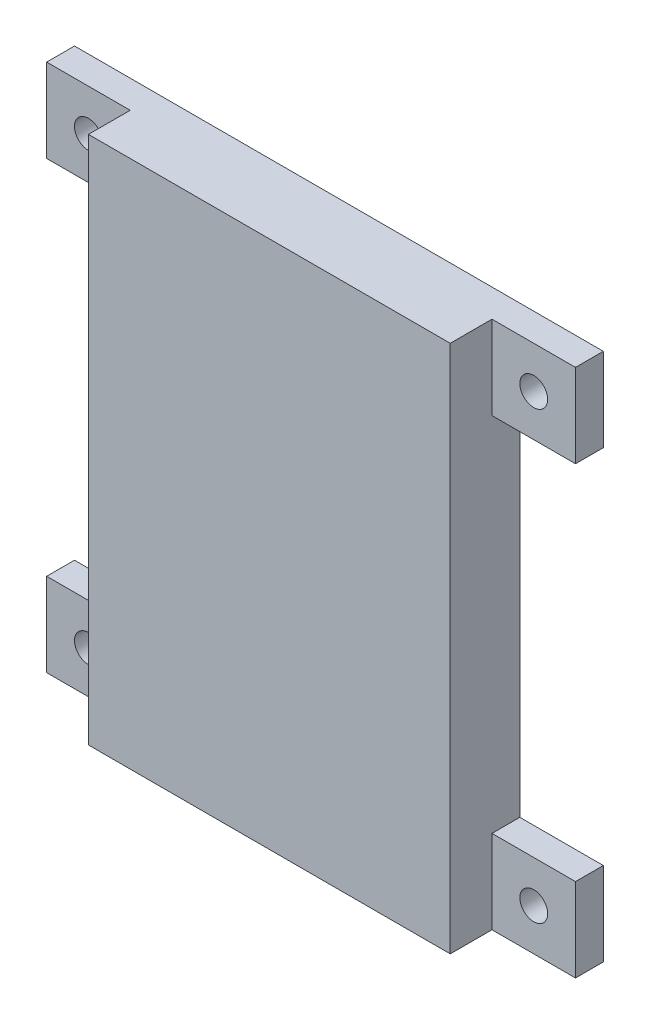
SolidWorks part; units mm, degrees
ref_plane "正面" through (0, 0, 0) normal (0, 0, 1) x (1, 0, 0)
ref_plane "平面" through (0, 0, 0) normal (0, 1, 0) x (1, 0, 0)
ref_plane "右側面" through (0, 0, 0) normal (1, 0, 0) x (0, 0, -1)
sketch "ｽｹｯﾁ1" plane through (0, 0, 0) normal (0, 0, 1) x (1, 0, 0)
  line L1 (13, -19) -> (-13, -19)
  line L2 (13, -19) -> (13, 19)
  line L3 (13, 19) -> (-13, 19)
  line L4 (-13, -19) -> (-13, 19)
  line L5 (13, -19) -> (-13, 19) construction
  line L6 (13, 19) -> (-13, -19) construction
  point P0 (0, 0)
  dimension "D1" = 38
  dimension "D2" = 26
extrude "ﾎﾞｽ - 押し出し1" add sketch "ｽｹｯﾁ1" along normal blind 5
sketch "ｽｹｯﾁ2" plane through (0, 0, 0) normal (0, 0, 1) x (1, 0, 0)
  line L1 (11, -17) -> (-11, -17)
  line L2 (11, -17) -> (11, 17)
  line L3 (11, 17) -> (-11, 17)
  line L4 (-11, -17) -> (-11, 17)
  line L5 (11, -17) -> (-11, 17) construction
  line L6 (11, 17) -> (-11, -17) construction
  point P0 (0, 0)
  dimension "D1" = 22
  dimension "D2" = 34
extrude "ｶｯﾄ - 押し出し1" cut sketch "ｽｹｯﾁ2" along normal blind 3
sketch "ｽｹｯﾁ3" plane through (0, 0, 0) normal (0, 0, 1) x (1, 0, 0)
  line L0 (13, 19) -> (-13, 19) construction
  line L1 (-0.8522, 2) -> (1.1478, 2)
  line L2 (-0.8522, 2) -> (-0.8522, 9)
  line L3 (-0.8522, 9) -> (1.1478, 9)
  line L4 (1.1478, 2) -> (1.1478, 9)
  line L5 (-0.8522, 2) -> (1.1478, 9) construction
  line L6 (-0.8522, 9) -> (1.1478, 2) construction
  point P0 (0.1478, 5.5)
  dimension "D1" = 7
  dimension "D2" = 2
  dimension "D3" = 10
sketch "ｽｹｯﾁ4" plane through (0, 0, 0) normal (0, 0, 1) x (1, 0, 0)
  line L0 (13, -19) -> (13, 19) construction
  line L1 (13, 19) -> (19, 19)
  line L2 (13, 19) -> (13, 13)
  line L3 (13, 13) -> (19, 13)
  line L4 (19, 19) -> (19, 13)
  line L5 (13, -19) -> (19, -19)
  line L6 (13, -19) -> (13, -13)
  line L7 (13, -13) -> (19, -13)
  line L8 (19, -19) -> (19, -13)
  line L9 (-13, -19) -> (13, -19) construction
  line L10 (-13, -19) -> (-19, -19)
  line L11 (-13, -19) -> (-13, -13)
  line L12 (-13, -13) -> (-19, -13)
  line L13 (-19, -19) -> (-19, -13)
  line L14 (-13, 19) -> (-19, 19)
  line L15 (-13, 19) -> (-13, 13)
  line L16 (-13, 13) -> (-19, 13)
  line L17 (-19, 19) -> (-19, 13)
  dimension "D1" = 6
  dimension "D2" = 6
  dimension "D3" = 6
  dimension "D4" = 6
  dimension "D5" = 6
  dimension "D6" = 6
  dimension "D7" = 6
  dimension "D8" = 6
  dimension "D9" = 0
extrude "ﾎﾞｽ - 押し出し2" add sketch "ｽｹｯﾁ4" along normal blind 2
sketch "ｽｹｯﾁ5" plane through (0, 0, 0) normal (0, 0, 1) x (1, 0, 0)
  line L0 (-13, 19) -> (-19, 19) construction
  line L1 (-19, 19) -> (-19, 13) construction
  line L2 (-13, -13) -> (-19, -13) construction
  line L3 (19, -19) -> (19, -13) construction
  line L4 (-19, -13) -> (-19, -19) construction
  line L5 (19, -13) -> (13, -13) construction
  line L6 (19, 13) -> (19, 19) construction
  line L7 (19, 19) -> (13, 19) construction
  circle A0 centre (-16, 16) radius 1
  circle A1 centre (-16, -16) radius 1
  circle A2 centre (16, -16) radius 1
  circle A3 centre (16, 16) radius 1
  dimension "D1" = 3
  dimension "D2" = 3
  dimension "D3" = 3
  dimension "D4" = 2
  dimension "D5" = 2
  dimension "D6" = 3
  dimension "D7" = 2
  dimension "D8" = 2
  dimension "D9" = 3
  dimension "D10" = 3
  dimension "D11" = 3
  dimension "D12" = 3
extrude "ｶｯﾄ - 押し出し4" cut sketch "ｽｹｯﾁ5" along normal blind 2
